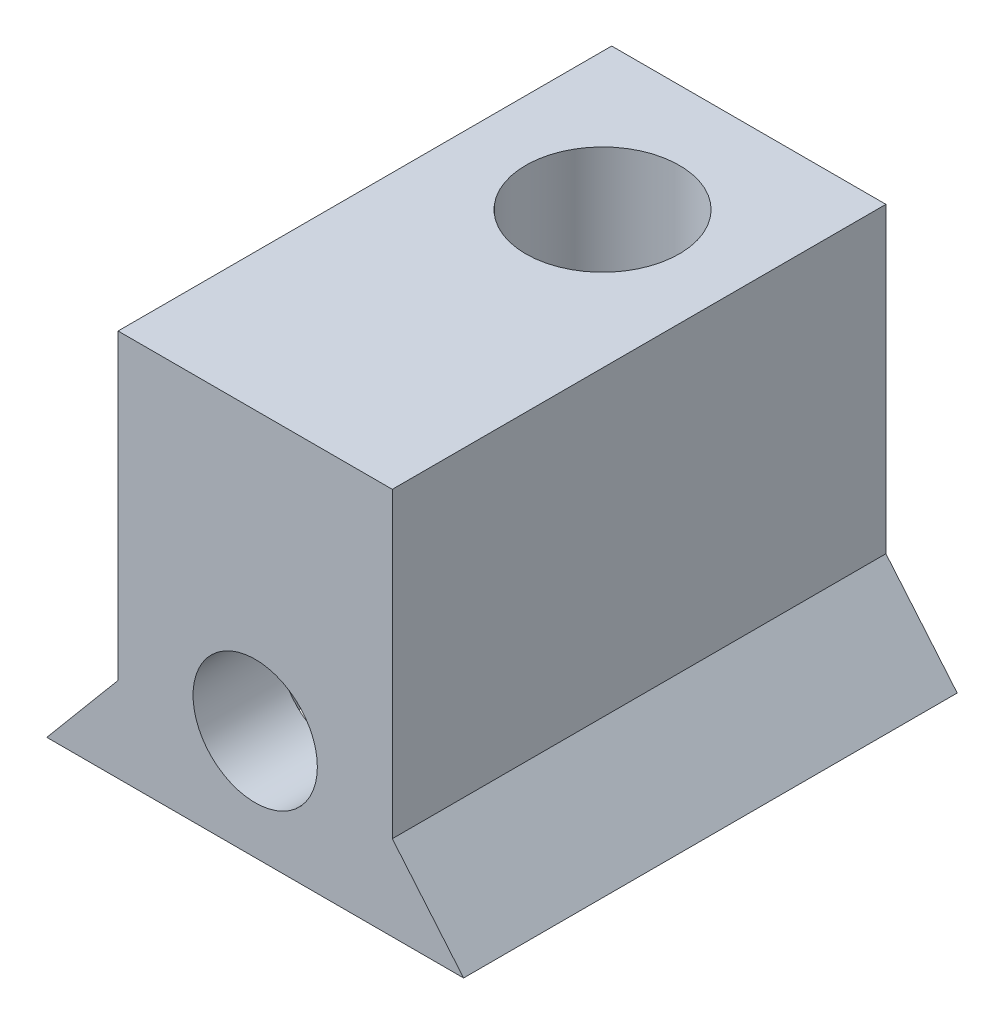
SolidWorks part; units mm, degrees
ref_plane "Alzado" through (0, 0, 0) normal (0, 0, 1) x (1, 0, 0)
ref_plane "Planta" through (0, 0, 0) normal (0, 1, 0) x (1, 0, 0)
ref_plane "Vista lateral" through (0, 0, 0) normal (1, 0, 0) x (0, 0, -1)
sketch "Croquis1" plane through (0, 0, 0) normal (0, 0, 1) x (1, 0, 0)
  line L0 (-5.7, 0) -> (5.7, 0)
  line L1 (5.7, 0) -> (3.75, 2.3239)
  line L2 (3.75, 2.3239) -> (3.75, 10.6)
  line L3 (3.75, 10.6) -> (-3.75, 10.6)
  line L4 (0, 20.1747) -> (0, -20.1747) construction
  line L5 (-3.75, 2.3239) -> (-3.75, 10.6)
  line L6 (-5.7, 0) -> (-3.75, 2.3239)
  circle A0 centre (0, 3) radius 1.7
  point P7 (0, 0)
  point P14 (0, 10.6)
  point P16 (0, 0)
  dimension "D6" = 3.4
  dimension "D1" = 3.75
  dimension "D2" = 5.7
  dimension "D3" = 10.6
  dimension "D4" = 50
  dimension "D5" = 3
extrude "Saliente-Extruir1" add sketch "Croquis1" along normal blind 13.5
sketch "Croquis2" plane through (0, 10.6, 0) normal (0, 1, 0) x (1, 0, 0)
  circle A0 centre (0, -4) radius 2.1
  point P2 (0, 0)
  dimension "D2" = 4.2
  dimension "D1" = 4
extrude "Cortar-Extruir1" cut sketch "Croquis2" against normal blind 5.1
ref_plane "Plano1" through (0, 0, 9.65) normal (0, 0, 1) x (1, 0, 0)
sketch "Croquis3" plane through (0, 0, 9.65) normal (0, 0, 1) x (1, 0, 0)
  line L0 (-2.9012, 1.325) -> (-2.9012, -5.325)
  line L1 (0, 6.35) -> (-2.9012, 4.675)
  line L2 (-2.9012, 4.675) -> (-2.9012, 1.325)
  line L3 (-2.9012, 1.325) -> (0, -0.35) construction
  line L4 (0, -0.35) -> (2.9012, 1.325) construction
  line L5 (2.9012, 1.325) -> (2.9012, 4.675)
  line L6 (2.9012, 4.675) -> (0, 6.35)
  line L7 (-2.9012, -5.325) -> (2.9012, -5.325)
  line L8 (2.9012, -5.325) -> (2.9012, 1.325)
  line L9 (-3.75, 10.6) -> (-3.75, 2.3239) construction
  circle A0 centre (0, 3) radius 3.35 construction
  dimension "D1" = 6.7
  dimension "D2" = 10
extrude "Cortar-Extruir2" cut sketch "Croquis3" against normal blind 1.5 and the other way blind 1.5
